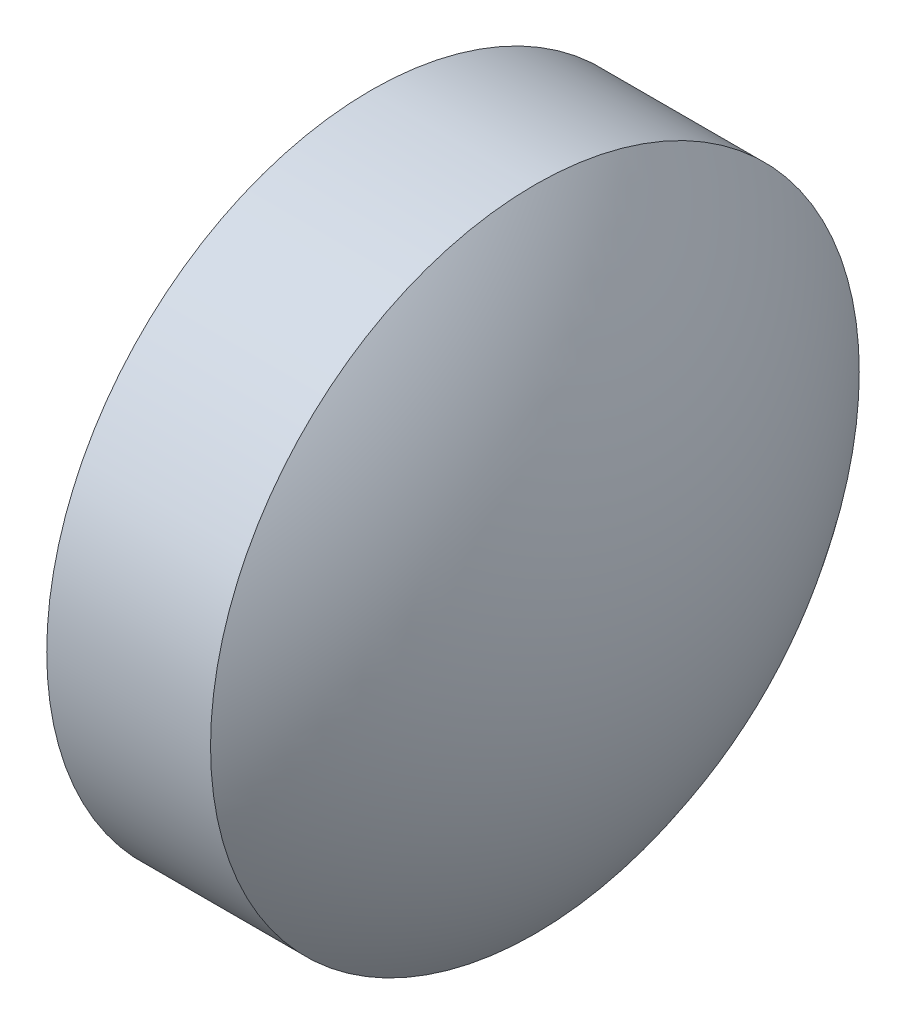
SolidWorks part; units mm, degrees
ref_plane "前视基准面" through (0, 0, 0) normal (0, 0, 1) x (1, 0, 0)
ref_plane "上视基准面" through (0, 0, 0) normal (0, 1, 0) x (1, 0, 0)
ref_plane "右视基准面" through (0, 0, 0) normal (1, 0, 0) x (0, 0, -1)
sketch "草图1" plane through (0, 0, 0) normal (0, 0, 1) x (1, 0, 0)
  line L0 (389.3827, 21.6854) -> (387.6827, 21.6854)
  line L6 (387.3355, 21.6854) -> (390.4032, 21.6854) construction
  line L7 (387.6827, 21.6854) -> (387.6827, 23.6854)
  line L11 (387.6827, 23.6854) -> (388.6927, 23.6854)
  arc A1 (389.3827, 21.6854) -> (388.6927, 23.6854) centre (386.1392, 21.6854) ccw
revolve "旋转1" add sketch "草图1" angle 360 about L6
